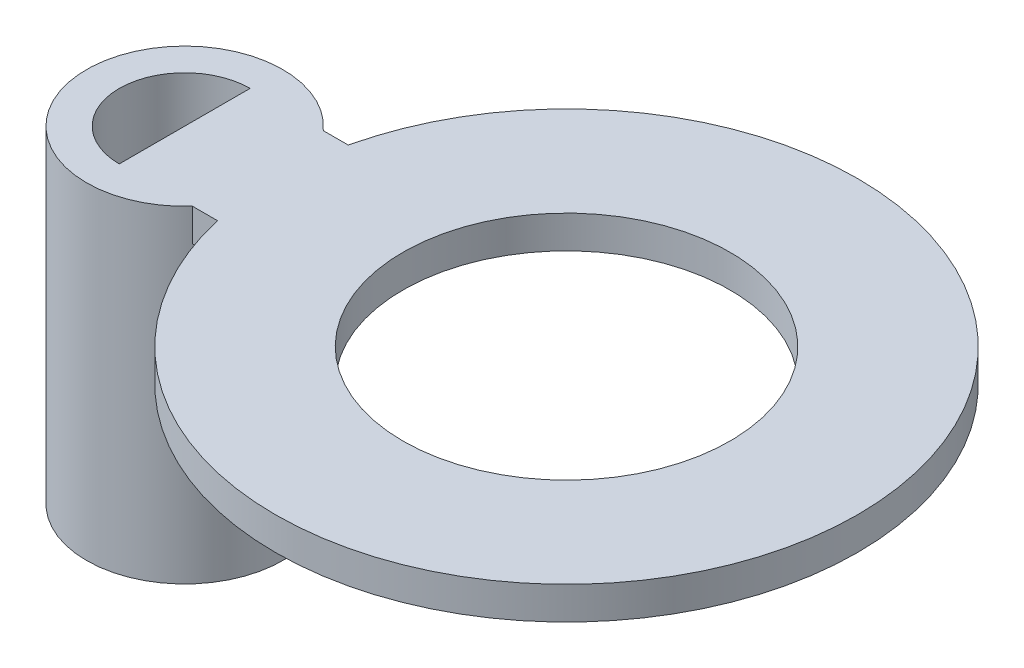
SolidWorks part; units mm, degrees
ref_plane "Front Plane" through (0, 0, 0) normal (0, 0, 1) x (1, 0, 0)
ref_plane "Top Plane" through (0, 0, 0) normal (0, 1, 0) x (1, 0, 0)
ref_plane "Right Plane" through (0, 0, 0) normal (1, 0, 0) x (0, 0, -1)
sketch "Sketch1" plane through (0, 0, 0) normal (0, 1, 0) x (1, 0, 0)
  line L0 (0, -1) -> (0, 1)
  line L1 (0, 1) -> (1.5, 1)
  line L2 (0, -1) -> (1.5, -1)
  arc A0 (1.5, -1) -> (1.5, 1) centre (5.8362, 0) ccw
  circle A1 centre (5.8362, 0) radius 2.5
  point P8 (0, 0)
  dimension "D1" = 5
  dimension "D2" = 8.9
  dimension "D3" = 1.5
  dimension "D4" = 2
extrude "Boss-Extrude1" add sketch "Sketch1" along normal blind 0.5
sketch "Sketch2" plane through (0.5, 0.5, 0) normal (0, 1, 0) x (0, 0, -1)
  line L0 (1, 0.5) -> (-1, 0.5) construction
  circle A0 centre (0, 0.5) radius 1.5
  circle A1 centre (0, 0.5) radius 1
  dimension "D1" = 2
  dimension "D2" = 3
extrude "Boss-Extrude2" add sketch "Sketch2" against normal blind 5
